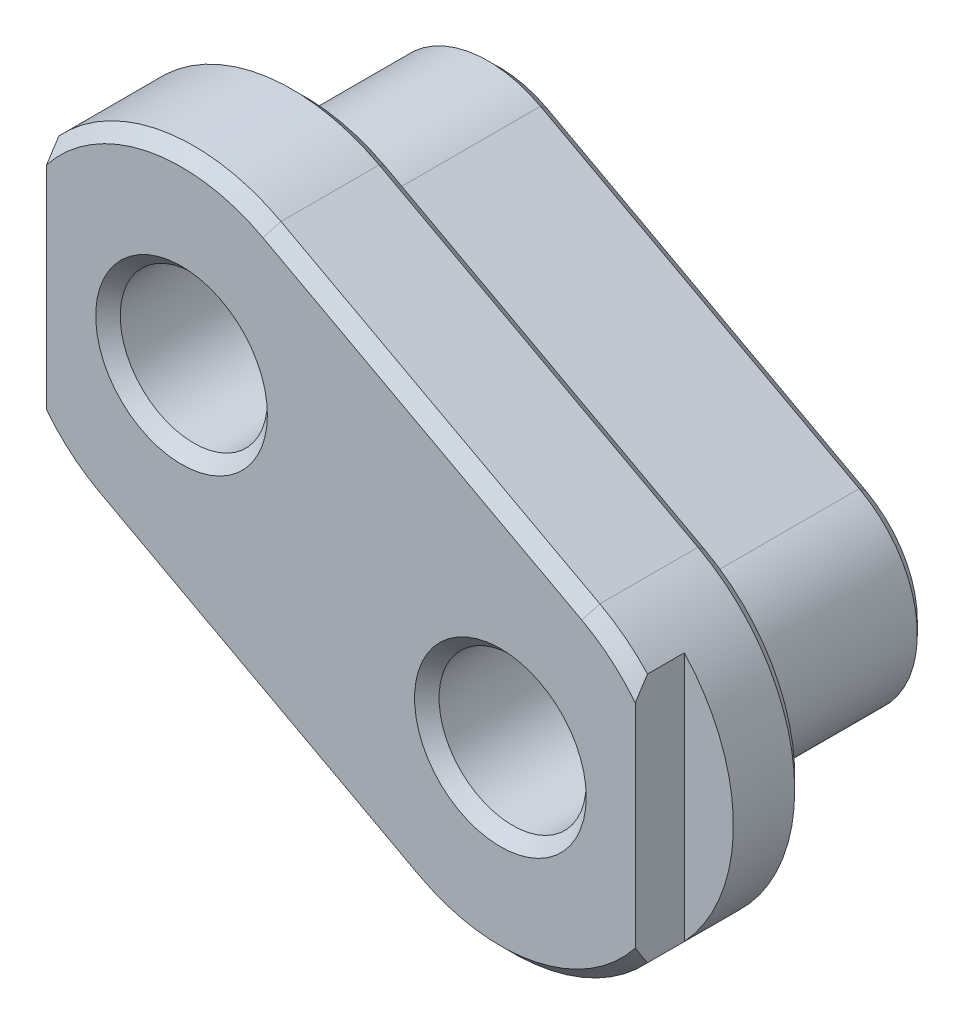
SolidWorks part; units mm, degrees
material "AISI 1020 钢，冷轧"
ref_plane "前视基准面" through (0, 0, 0) normal (0, 0, 1) x (1, 0, 0)
ref_plane "上视基准面" through (0, 0, 0) normal (0, 1, 0) x (1, 0, 0)
ref_plane "右视基准面" through (0, 0, 0) normal (1, 0, 0) x (0, 0, -1)
sketch "草图1" plane through (0, 0, 0) normal (0, 0, 1) x (1, 0, 0)
  line L0 (-30.2669, 6.0758) -> (-4.2669, -7.9242)
  line L1 (-21.7331, 21.9242) -> (4.2669, 7.9242)
  line L4 (0, 0) -> (-26, 0) construction
  line L5 (-26, 14) -> (-26, 0) construction
  line L6 (-26, 14) -> (0, 0) construction
  arc A0 (-21.7331, 21.9242) -> (-30.2669, 6.0758) centre (-26, 14) ccw
  arc A1 (-4.2669, -7.9242) -> (4.2669, 7.9242) centre (0, 0) ccw
  dimension "D3" = 9
  dimension "D4" = 9
  dimension "D1" = 14
  dimension "D2" = 26
extrude "凸台-拉伸1" add sketch "草图1" along normal blind 16
sketch "草图2" plane through (0, 0, 16) normal (0, 0, 1) x (1, 0, 0)
  line L7 (7.1115, 13.2071) -> (-18.8885, 27.2071)
  line L8 (-33.1115, 0.7929) -> (-7.1115, -13.2071)
  line L9 (7.1115, 13.2071) -> (-18.8885, 27.2071)
  line L10 (-33.1115, 0.7929) -> (-7.1115, -13.2071)
  arc A7 (-7.1115, -13.2071) -> (7.1115, 13.2071) centre (0, 0) ccw
  arc A8 (-18.8885, 27.2071) -> (-33.1115, 0.7929) centre (-26, 14) ccw
  arc A9 (-7.1115, -13.2071) -> (7.1115, 13.2071) centre (0, 0) ccw
  arc A10 (-18.8885, 27.2071) -> (-33.1115, 0.7929) centre (-26, 14) ccw
  dimension "D1" = 6
extrude "凸台-拉伸2" add sketch "草图2" along normal blind 10
sketch "草图3" plane through (0, 0, 26) normal (0, 0, 1) x (1, 0, 0)
  line L0 (-37, 24.198) -> (-37, 3.802)
  line L1 (11, 10.198) -> (11, -10.198)
  line L4 (7.1115, 13.2071) -> (-18.8885, 27.2071)
  line L5 (-33.1115, 0.7929) -> (-7.1115, -13.2071)
  arc A0 (-18.8885, 27.2071) -> (-33.1115, 0.7929) centre (-26, 14) ccw construction
  arc A3 (-7.1115, -13.2071) -> (7.1115, 13.2071) centre (0, 0) ccw
  arc A4 (-18.8885, 27.2071) -> (-33.1115, 0.7929) centre (-26, 14) ccw
  arc A5 (11, -10.198) -> (11, 10.198) centre (0, 0) ccw
  arc A6 (-37, 24.198) -> (-37, 3.802) centre (-26, 14) ccw
  dimension "D1" = 11
  dimension "D2" = 0
  dimension "D3" = 11
extrude "切除-拉伸1" cut sketch "草图3" against normal blind 4
sketch "草图4" plane through (0, 0, 0) normal (0, 0, -1) x (-1, 0, 0)
  circle A0 centre (0, 0) radius 6
  circle A1 centre (26, 14) radius 6
  dimension "D1" = 12
  dimension "D2" = 12
extrude "切除-拉伸2" cut sketch "草图4" against normal through all
chamfer "倒角1" distance 1 angle 45 18 edges at (-8.7331, 14.9242, 0) (-33.9242, 18.2669, 0) (-17.2669, -0.9242, 0) (7.9242, -4.2669, 0) (-32, 14, 0) (-6, 0, 0) (-32, 14, 26) (-6, 0, 26) (-35.1799, 2.137, 26) (-20.1115, -6.2071, 26) (2.4584, -14.7972, 26) (9.1799, 11.863, 26) (-5.8885, 20.2071, 26) (-28.4584, 28.7972, 26) (13.2071, -7.1115, 16) (-5.8885, 20.2071, 16) (-20.1115, -6.2071, 16) (-39.2071, 21.1115, 16)
